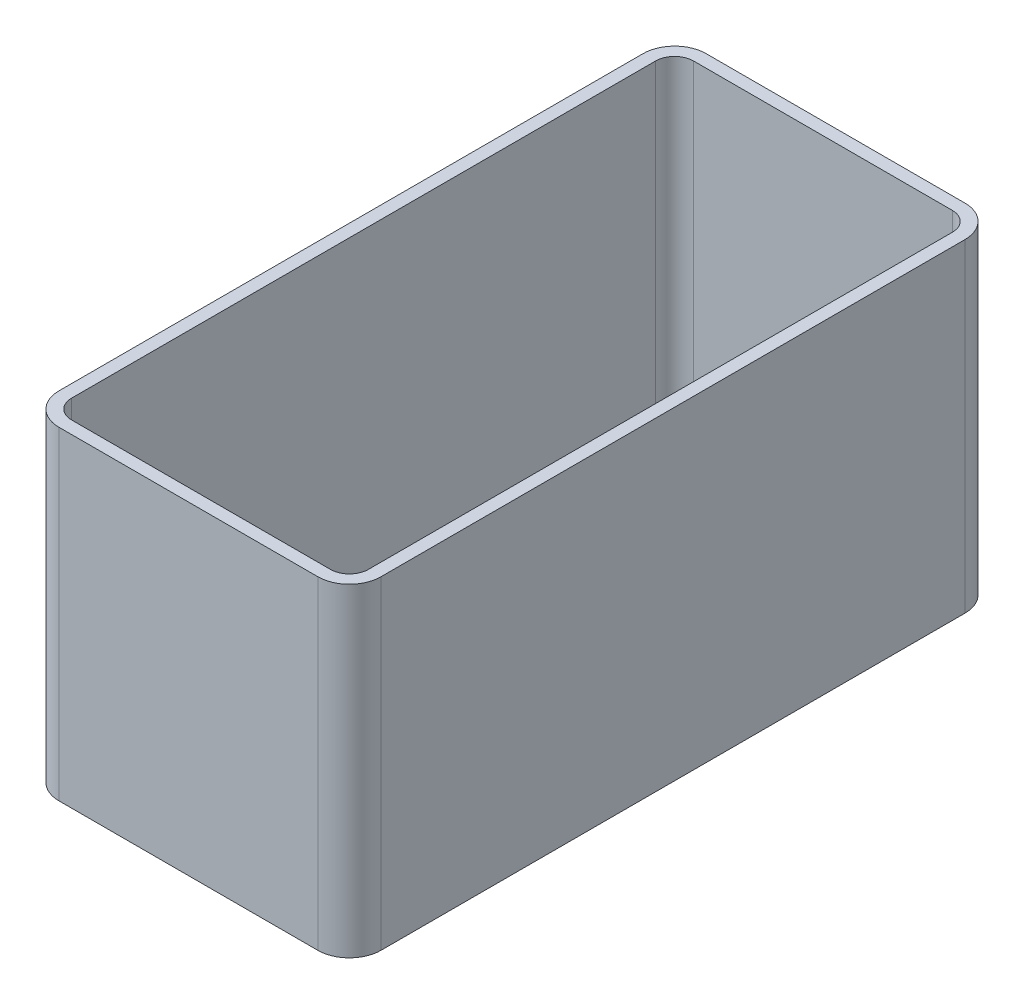
SolidWorks part; units mm, degrees
material "PC High Viscosity"
ref_plane "Front Plane" through (0, 0, 0) normal (0, 0, 1) x (1, 0, 0)
ref_plane "Top Plane" through (0, 0, 0) normal (0, 1, 0) x (1, 0, 0)
ref_plane "Right Plane" through (0, 0, 0) normal (1, 0, 0) x (0, 0, -1)
sketch "BaseS" plane through (0, 0, 0) normal (0, 1, 0) x (1, 0, 0)
  line L1 (-10.2, 20.5) -> (10.2, 20.5)
  line L2 (-10.2, 20.5) -> (-10.2, -20.5)
  line L3 (-10.2, -20.5) -> (10.2, -20.5)
  line L4 (10.2, 20.5) -> (10.2, -20.5)
  line L5 (-10.2, 20.5) -> (10.2, -20.5) construction
  line L6 (-10.2, -20.5) -> (10.2, 20.5) construction
  point P0 (0, 0)
  dimension "D1" = 20.4
  dimension "D2" = 41
extrude "BASE" add sketch "BaseS" along normal mid plane 20.5
fillet "BASE F" radius 2 4 edges at (-10.2, 0, -20.5) (10.2, 0, -20.5) (10.2, 0, 20.5) (-10.2, 0, 20.5)
sketch "PocketS" plane through (0, 10.25, 0) normal (0, 1, 0) x (1, 0, 0)
  line L0 (8.2, 19.7) -> (-8.2, 19.7)
  line L1 (-9.4, 18.5) -> (-9.4, -18.5)
  line L2 (-8.2, -19.7) -> (8.2, -19.7)
  line L3 (9.4, -18.5) -> (9.4, 18.5)
  line L4 (8.2, 20.5) -> (-8.2, 20.5)
  line L5 (-10.2, 18.5) -> (-10.2, -18.5)
  line L6 (-8.2, -20.5) -> (8.2, -20.5)
  line L7 (10.2, -18.5) -> (10.2, 18.5)
  line L8 (8.2, 20.5) -> (-8.2, 20.5) construction
  line L9 (-10.2, 18.5) -> (-10.2, -18.5) construction
  line L10 (-8.2, -20.5) -> (8.2, -20.5) construction
  line L11 (10.2, -18.5) -> (10.2, 18.5) construction
  arc A0 (-8.2, 19.7) -> (-9.4, 18.5) centre (-8.2, 18.5) ccw
  arc A1 (-9.4, -18.5) -> (-8.2, -19.7) centre (-8.2, -18.5) ccw
  arc A2 (8.2, -19.7) -> (9.4, -18.5) centre (8.2, -18.5) ccw
  arc A3 (9.4, 18.5) -> (8.2, 19.7) centre (8.2, 18.5) ccw
  arc A4 (-8.2, 20.5) -> (-10.2, 18.5) centre (-8.2, 18.5) ccw
  arc A5 (-10.2, -18.5) -> (-8.2, -20.5) centre (-8.2, -18.5) ccw
  arc A6 (8.2, -20.5) -> (10.2, -18.5) centre (8.2, -18.5) ccw
  arc A7 (10.2, 18.5) -> (8.2, 20.5) centre (8.2, 18.5) ccw
  arc A8 (-8.2, 20.5) -> (-10.2, 18.5) centre (-8.2, 18.5) ccw construction
  arc A9 (-10.2, -18.5) -> (-8.2, -20.5) centre (-8.2, -18.5) ccw construction
  arc A10 (8.2, -20.5) -> (10.2, -18.5) centre (8.2, -18.5) ccw construction
  arc A11 (10.2, 18.5) -> (8.2, 20.5) centre (8.2, 18.5) ccw construction
  dimension "D1" = 0
  dimension "D2" = 0.8
extrude "Cut-Extrude3" cut sketch "PocketS" against normal through all
